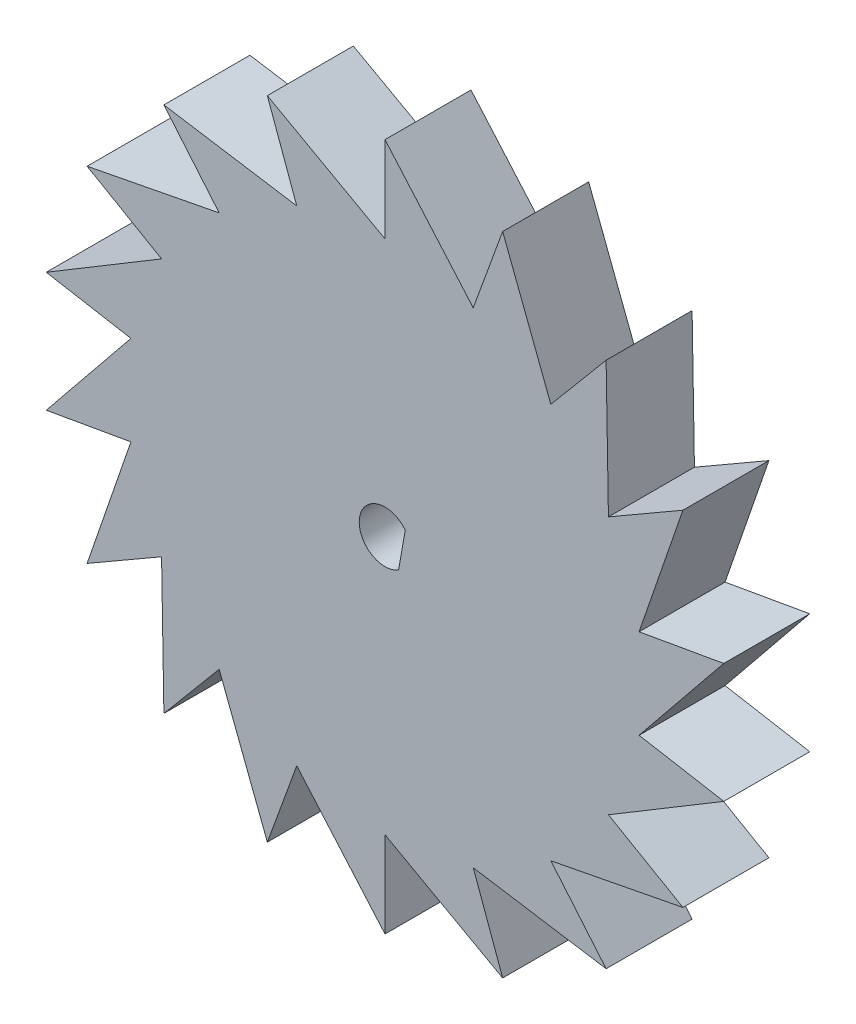
SolidWorks part; units mm, degrees
ref_plane "Front Plane" through (0, 0, 0) normal (0, 0, 1) x (1, 0, 0)
ref_plane "Top Plane" through (0, 0, 0) normal (0, 1, 0) x (1, 0, 0)
ref_plane "Right Plane" through (0, 0, 0) normal (1, 0, 0) x (0, 0, -1)
sketch "Sketch1" plane through (0, 0, 0) normal (0, 0, 1) x (1, 0, 0)
  line L0 (0, 0) -> (0, 20)
  line L3 (5.1303, 14.0954) -> (0, 0)
  line L4 (5.1303, 14.0954) -> (0, 20)
  dimension "D1" = 20
  dimension "D2" = 15
  dimension "D3" = 20
extrude "Boss-Extrude1" add sketch "Sketch1" along normal blind 5
pattern_circular "CirPattern1" count 18 every 20 about axis through (0, 0, 0) along (0, 0, 1) of "Boss-Extrude1"
sketch "Sketch7" plane through (0, 0, 0) normal (0, 0, -1) x (-1, 0, 0)
  circle A0 centre (0, 0) radius 4
  dimension "D1" = 8
extrude "Boss-Extrude3" add sketch "Sketch7" along normal blind 5
sketch "Sketch2" plane through (0, 0, 5) normal (0, 0, 1) x (1, 0, 0)
  line L0 (1.3896, 2.1214) -> (0.6326, -2.1704)
  circle A0 centre (0, 0) radius 1.45
  dimension "D1" = 2.9
  dimension "D2" = 1
sketch "Sketch5" plane through (0, 0, 5) normal (0, 0, 1) x (1, 0, 0)
  line L0 (1.179, 0.9273) -> (0.7906, -1.2747)
  line L1 (1.3896, 2.1214) -> (0.6326, -2.1704) construction
  arc A1 (0.7906, -1.2747) -> (1.179, 0.9273) centre (0, 0) cw
extrude "Cut-Extrude1" cut sketch "Sketch5" against normal up to surface (10 mm away) up to face at (-4, 0, -5)
